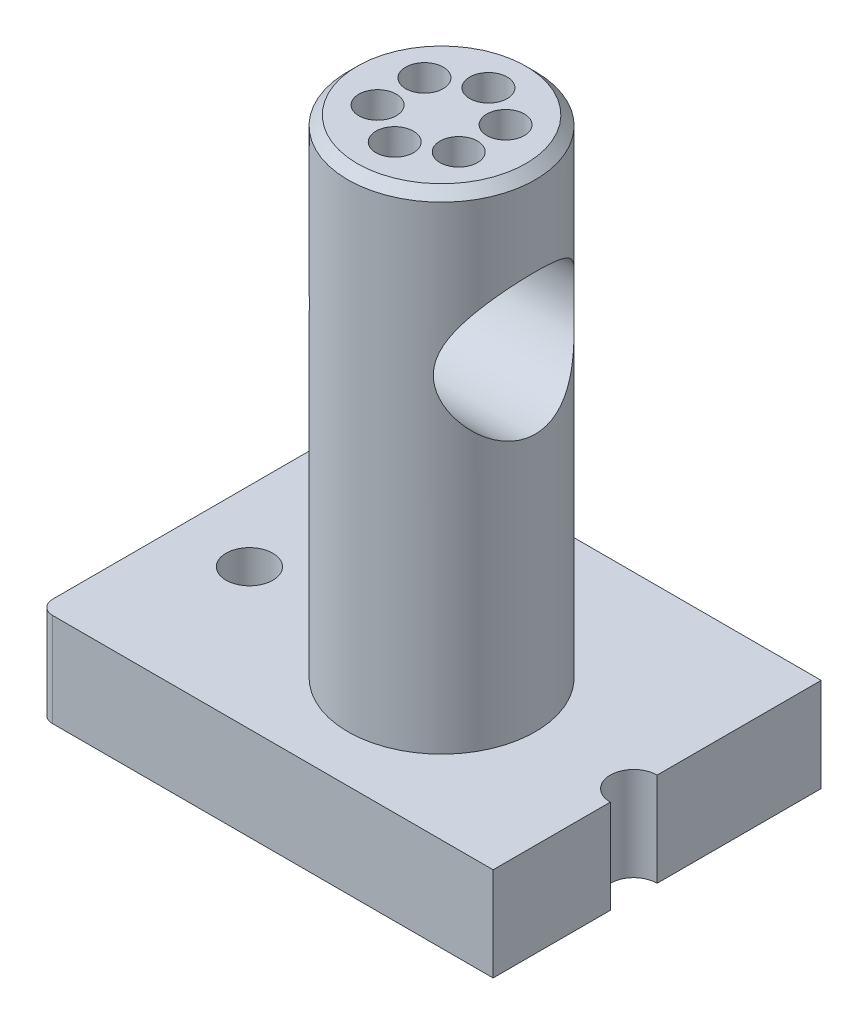
SolidWorks part; units mm, degrees
ref_plane "Front Plane" through (0, 0, 0) normal (0, 0, 1) x (1, 0, 0)
ref_plane "Top Plane" through (0, 0, 0) normal (0, 1, 0) x (1, 0, 0)
ref_plane "Right Plane" through (0, 0, 0) normal (1, 0, 0) x (0, 0, -1)
sketch "Sketch1" plane through (0, 0, 0) normal (0, 1, 0) x (1, 0, 0)
  line L0 (-33.5, -5) -> (48.5, -5) construction
  line L1 (-45.5, 35) -> (48.5, 35)
  line L2 (-48.5, 32) -> (-48.5, -32)
  line L3 (-45.5, -35) -> (48.5, -35)
  line L4 (48.5, 35) -> (48.5, 0)
  line L5 (-48.5, 35) -> (48.5, -35) construction
  line L6 (-48.5, -35) -> (48.5, 35) construction
  line L7 (7.5, 15) -> (7.5, -25) construction
  line L8 (-12.5, -5) -> (27.5, -5) construction
  line L9 (48.5, -10) -> (48.5, -35)
  arc A0 (-48.5, -32) -> (-45.5, -35) centre (-45.5, -32) ccw
  arc A1 (-45.5, 35) -> (-48.5, 32) centre (-45.5, 32) ccw
  circle A3 centre (-33.5, -5) radius 5
  circle A4 centre (7.5, -5) radius 20
  circle A5 centre (7.5, -5) radius 10 construction
  circle A7 centre (-33.5, -5) radius 9
  arc A8 (48.5, 0) -> (48.5, -10) centre (48.5, -5) ccw
  point P0 (0, 0)
  dimension "D3" = 3
  dimension "D4" = 30
  dimension "D6" = 10
  dimension "D7" = 40
  dimension "D9" = 20
  dimension "D10" = 18
  dimension "D11" = 10
  dimension "D1" = 70
  dimension "D2" = 97
  dimension "D5" = 15
  dimension "D8" = 56
extrude "Boss-Extrude1" add sketch "Sketch1" along normal blind 20 contours A4 | L2 A0 L3 L9 A8 L4 L1 A1
sketch "Sketch2" plane through (0, 0, 0) normal (0, -1, 0) x (1, 0, 0)
  circle A0 centre (-33.5, 5) radius 5 construction
  circle A1 centre (-33.5, 5) radius 5
extrude "Cut-Extrude1" cut sketch "Sketch2" against normal through all
sketch "Sketch3" plane through (0, 0, 0) normal (0, -1, 0) x (1, 0, 0)
  circle A0 centre (-33.5, 5) radius 9 construction
  circle A1 centre (-33.5, 5) radius 9
extrude "Cut-Extrude2" cut sketch "Sketch3" against normal blind 10
sketch "Sketch4" plane through (0, 20, 0) normal (0, 1, 0) x (1, 0, 0)
  circle A0 centre (7.5, -5) radius 20 construction
  circle A1 centre (7.5, -5) radius 20
  circle A2 centre (7.5, -5) radius 10 construction
  circle A3 centre (7.5, -5) radius 10 construction
extrude "Boss-Extrude2" add sketch "Sketch4" along normal blind 104 and the other way up to surface (20 mm away) separate body other way up to face at (-33.5, 0, -4)
sketch "Sketch5" plane through (0, 0, 0) normal (1, 0, 0) x (0, 0, -1)
  line L0 (-5, 124) -> (-5, 20) construction
  line L2 (15, 124) -> (-25, 124) construction
  line L5 (35, 20) -> (0, 20) construction
  circle A0 centre (-5, 90) radius 15
  dimension "D1" = 30
  dimension "D2" = 70
extrude "Cut-Extrude3" cut sketch "Sketch5" against normal through all both and the other way through all
chamfer "Chamfer1" distance 2 angle 45 1 edges at (7.5, 124, 25)
sketch "Sketch6" plane through (0, 124, 0) normal (0, 1, 0) x (1, 0, 0)
  circle A0 centre (7.5, -5) radius 10 construction
  circle A1 centre (7.5, -5) radius 10 construction
  circle A2 centre (7.5, 5) radius 4
  circle A3 centre (16.1603, 0) radius 4
  circle A4 centre (16.1603, -10) radius 4
  circle A5 centre (7.5, -15) radius 4
  circle A6 centre (-1.1603, -10) radius 4
  circle A7 centre (-1.1603, 0) radius 4
  dimension "D1" = 8
  dimension "D2" = 6
extrude "Cut-Extrude4" cut sketch "Sketch6" against normal up to surface (20.2523 mm away)
ref_plane "Plane1" through (0, 62, 0) normal (0, 1, 0) x (1, 0, 0)
